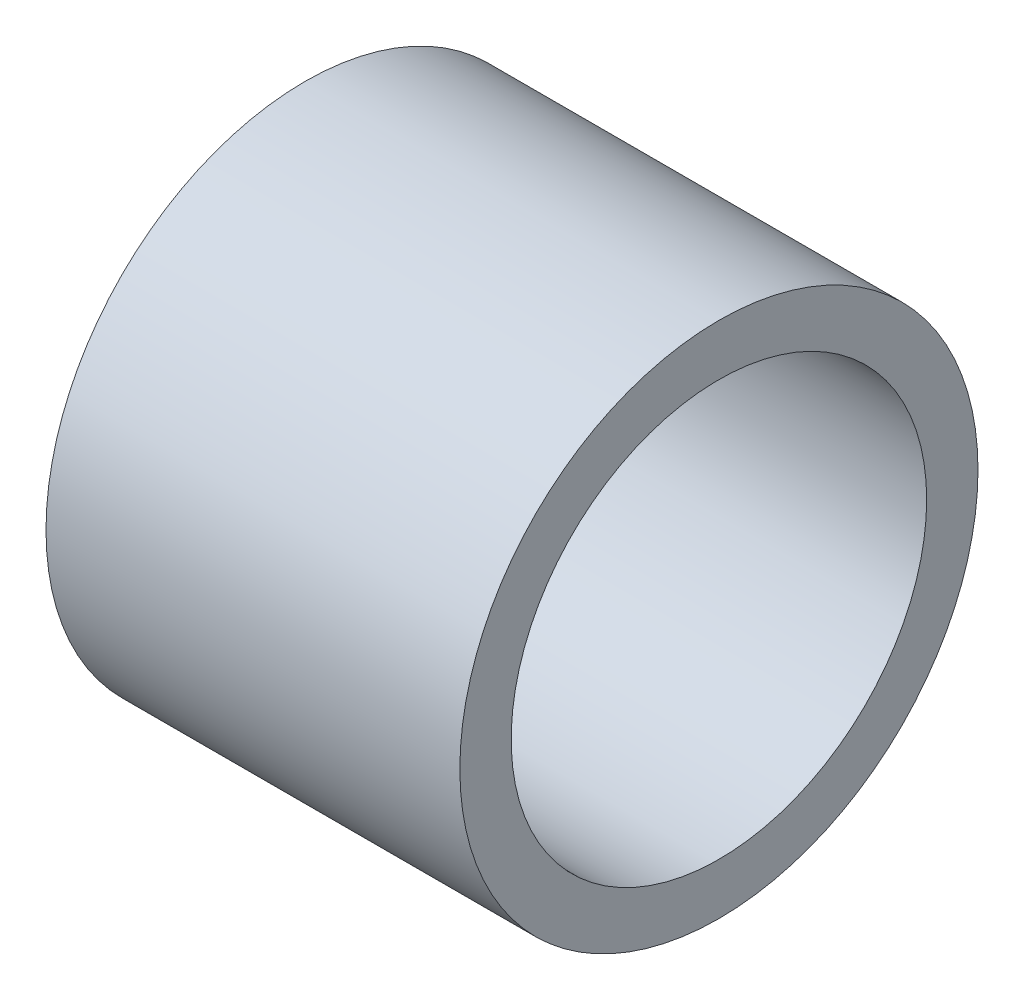
SolidWorks part; units mm, degrees
material "6061-T6 (SS)"
ref_plane "Front" through (0, 0, 0) normal (0, 0, 1) x (1, 0, 0)
ref_plane "Top" through (0, 0, 0) normal (0, 1, 0) x (1, 0, 0)
ref_plane "Right" through (0, 0, 0) normal (1, 0, 0) x (0, 0, -1)
sketch "Sketch1" plane through (0, 0, 0) normal (1, 0, 0) x (0, 0, -1)
  circle A0 centre (0, 0) radius 3.1877
  circle A1 centre (0, 0) radius 3.9751
  dimension "D1" = 6.3754
  dimension "D2" = 7.9502
extrude "Boss-Extrude1" add sketch "Sketch1" along normal mid plane 6.35
